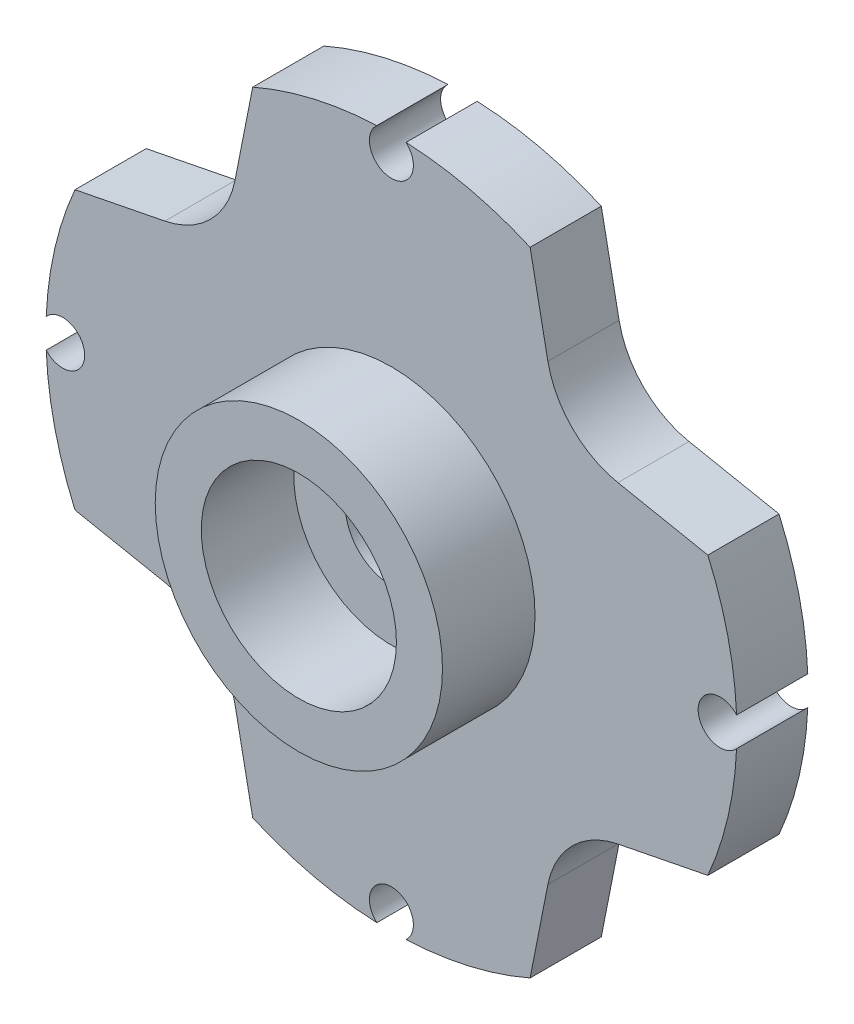
SolidWorks part; units mm, degrees
ref_plane "Front Plane" through (0, 0, 0) normal (0, 0, 1) x (1, 0, 0)
ref_plane "Top Plane" through (0, 0, 0) normal (0, 1, 0) x (1, 0, 0)
ref_plane "Right Plane" through (0, 0, 0) normal (1, 0, 0) x (0, 0, -1)
sketch "Sketch1" plane through (0, 0, 0) normal (0, 0, 1) x (1, 0, 0)
  line L0 (0, 0) -> (0, 13.35) construction
  line L1 (0, 13.35) -> (0, -13.35) construction
  line L2 (0, 0) -> (13.35, 0) construction
  line L3 (0, 0) -> (-13.35, 0) construction
  line L4 (0, 0) -> (-4.0128, 4.0128) construction
  line L5 (0, 0) -> (4.0128, 4.0128) construction
  line L6 (5.4091, 3.7367) -> (13.7623, 2.0848)
  line L7 (3.7367, 5.4091) -> (2.0848, 13.7623)
  line L8 (-3.7367, 5.4091) -> (-2.0848, 13.7623)
  line L9 (-5.4091, 3.7367) -> (-13.7623, 2.0848)
  line L12 (0, 0) -> (4.0128, -4.0128) construction
  line L13 (0, 0) -> (-4.0128, -4.0128) construction
  line L14 (-5.4091, -3.7367) -> (-13.7623, -2.0848)
  line L15 (-3.7367, -5.4091) -> (-2.0848, -13.7623)
  line L16 (3.7367, -5.4091) -> (2.0848, -13.7623)
  line L17 (5.4091, -3.7367) -> (13.7623, -2.0848)
  circle A0 centre (0, 0) radius 1.11
  arc A1 (3.7367, 5.4091) -> (5.4091, 3.7367) centre (5.8213, 5.8213) ccw
  arc A2 (13.7623, -2.0848) -> (13.7623, 2.0848) centre (13.35, 0) ccw
  arc A3 (2.0848, -13.7623) -> (-2.0848, -13.7623) centre (0, -13.35) cw
  arc A4 (-13.7623, 2.0848) -> (-13.7623, -2.0848) centre (-13.35, 0) ccw
  arc A5 (-3.7367, 5.4091) -> (-5.4091, 3.7367) centre (-5.8213, 5.8213) cw
  arc A6 (2.0848, 13.7623) -> (-2.0848, 13.7623) centre (0, 13.35) ccw
  arc A7 (-3.7367, -5.4091) -> (-5.4091, -3.7367) centre (-5.8213, -5.8213) ccw
  arc A8 (3.7367, -5.4091) -> (5.4091, -3.7367) centre (5.8213, -5.8213) cw
  point P17 (0, 0)
extrude "Boss-Extrude1" add sketch "Sketch1" along normal blind 1.7 contours L9 A4 L14 A7 L15 A3 L16 A8 L17 A2 L6 A1 L7 A6 L8 A5
sketch "Sketch2" plane through (0, 0, 1.7) normal (0, 0, 1) x (1, 0, 0)
  circle A0 centre (0, 0) radius 1.1
extrude "Cut-Extrude1" cut sketch "Sketch2" against normal up to next
sketch "Sketch3" plane through (0, 0, 1.7) normal (0, 0, 1) x (1, 0, 0)
  circle A0 centre (0, 0) radius 3.43
  circle A1 centre (0, 0) radius 2.33
  dimension "D1" = 1.1
extrude "Boss-Extrude2" add sketch "Sketch3" along normal blind 2.21
sketch "Sketch4" plane through (0, 0, 0) normal (0, 0, -1) x (-1, 0, 0)
  circle A0 centre (0, 0) radius 3.5
  circle A1 centre (0, 0) radius 2.95
  dimension "D1" = 0.55
extrude "Boss-Extrude3" add sketch "Sketch4" along normal blind 0.51
sketch "Sketch5" plane through (0, 0, -0.51) normal (0, 0, -1) x (-1, 0, 0)
  circle A0 centre (0, 0) radius 2.95
extrude "Cut-Extrude2" cut sketch "Sketch5" against normal blind 1.1
sketch "Sketch6" plane through (0, 0, 1.7) normal (0, 0, 1) x (1, 0, 0)
  circle A0 centre (0, 13.35) radius 0.525
  circle A1 centre (0, 10.6) radius 0.525
  circle A2 centre (0, 7.85) radius 0.525
  circle A3 centre (13.35, 0) radius 0.525
  circle A4 centre (10.6, 0) radius 0.525
  circle A5 centre (7.85, 0) radius 0.525
  circle A6 centre (0, -13.35) radius 0.525
  circle A7 centre (0, -10.6) radius 0.525
  circle A8 centre (0, -7.85) radius 0.525
  circle A9 centre (-13.35, 0) radius 0.525
  circle A10 centre (-10.6, 0) radius 0.525
  circle A11 centre (-7.85, 0) radius 0.525
  point P28 (0, 0)
  dimension "D1" = 3
  dimension "D2" = 4
extrude "Cut-Extrude3" cut sketch "Sketch6" against normal up to next
sketch "Sketch7" plane through (0, 0, 1.7) normal (0, 0, 1) x (1, 0, 0)
  circle A0 centre (0, 0) radius 8.25
  circle A1 centre (0, 0) radius 18.883
  dimension "D1" = 16.5
extrude "Cut-Extrude4" cut sketch "Sketch7" against normal through all both and the other way through all
